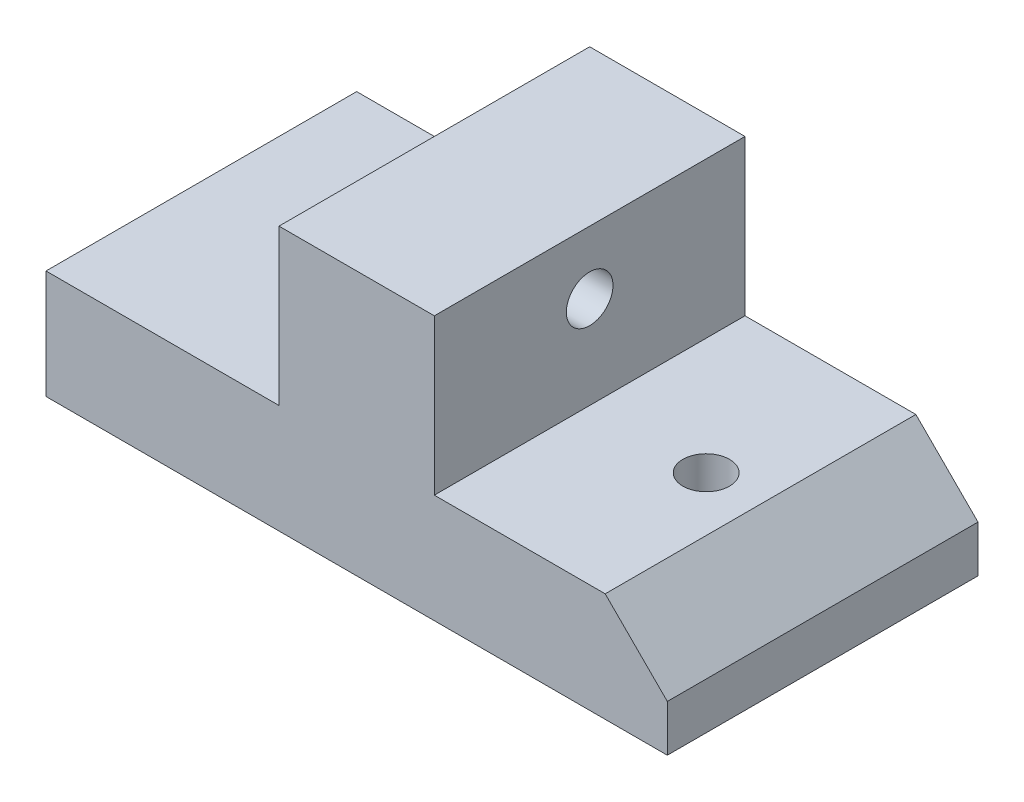
SolidWorks part; units mm, degrees
ref_plane "Front Plane" through (0, 0, 0) normal (0, 0, 1) x (1, 0, 0)
ref_plane "Top Plane" through (0, 0, 0) normal (0, 1, 0) x (1, 0, 0)
ref_plane "Right Plane" through (0, 0, 0) normal (1, 0, 0) x (0, 0, -1)
sketch "Sketch1" plane through (0, 0, 0) normal (0, 1, 0) x (1, 0, 0)
  line L5 (-34.4733, 11.0833) -> (5.5267, 11.0833)
  line L6 (-34.4733, 11.0833) -> (-34.4733, -8.9167)
  line L7 (-34.4733, -8.9167) -> (5.5267, -8.9167)
  line L8 (5.5267, 11.0833) -> (5.5267, -8.9167)
  dimension "D1" = 20
  dimension "D2" = 40
extrude "Boss-Extrude1" add sketch "Sketch1" along normal blind 4
sketch "Sketch2" plane through (0, 4, 0) normal (0, 1, 0) x (1, 0, 0)
  line L0 (-34.4733, -8.9167) -> (5.5267, 11.0833)
  line L1 (-34.4733, -8.9167) -> (5.5267, -8.9167) construction
  line L2 (-19.4733, 11.0833) -> (-9.4733, 11.0833)
  line L3 (-19.4733, 11.0833) -> (-19.4733, -8.9167)
  line L4 (-19.4733, -8.9167) -> (-9.4733, -8.9167)
  line L5 (-9.4733, 11.0833) -> (-9.4733, -8.9167)
  line L6 (-19.4733, 11.0833) -> (-9.4733, -8.9167) construction
  line L7 (-19.4733, -8.9167) -> (-9.4733, 11.0833) construction
  point P4 (-14.4733, 1.0833)
  dimension "D1" = 10
extrude "Boss-Extrude2" add sketch "Sketch2" along normal blind 10 contours L3 L2 L5 L4
sketch "Sketch3" plane through (-9.4733, 0, 0) normal (1, 0, 0) x (0, 0, -1)
  line L0 (-8.9167, 4) -> (11.0833, 4)
  line L1 (11.0833, 4) -> (1.0833, 4)
  circle A0 centre (1.0833, 9.951) radius 1.5
  dimension "D1" = 5.951
extrude "Cut-Extrude1" cut sketch "Sketch3" against normal blind 20 contours A0
sketch "Sketch4" plane through (0, 4, 0) normal (0, 1, 0) x (1, 0, 0)
  line L0 (-9.4733, -8.9167) -> (5.5267, 11.0833)
  line L1 (5.5267, 11.0833) -> (5.5267, -8.9167)
  circle A0 centre (-1.9733, 1.0833) radius 1.5
  circle A1 centre (-26.9733, 1.0833) radius 1.5
extrude "Cut-Extrude2" cut sketch "Sketch4" against normal blind 20 contours L0 A0 | L0 A0 | A1
sketch "Sketch5" plane through (0, 0, 8.9167) normal (0, 0, 1) x (1, 0, 0)
  line L0 (5.5267, 4) -> (1.5267, 4)
  line L1 (-9.4733, 4) -> (5.5267, 4) construction
  line L2 (1.5267, 4) -> (5.5267, 0)
extrude "Cut-Extrude3" cut sketch "Sketch5" against normal blind 20 and the other way through all
sketch "Sketch6" plane through (0, 0, 0) normal (0, -1, 0) x (1, 0, 0)
  line L1 (5.5267, 8.9167) -> (-34.4733, 8.9167)
  line L2 (5.5267, 8.9167) -> (5.5267, -11.0833)
  line L3 (5.5267, -11.0833) -> (-34.4733, -11.0833)
  line L4 (-34.4733, 8.9167) -> (-34.4733, -11.0833)
extrude "Boss-Extrude3" add sketch "Sketch6" along normal blind 4.5
sketch "Sketch7" plane through (0, 0, 0) normal (0, 1, 0) x (1, 0, 0)
  line L0 (-3.4733, 1.0833) -> (-0.4733, 1.0833)
  circle A0 centre (-1.9733, 1.0833) radius 1.5 construction
  circle A1 centre (-1.9733, 1.0833) radius 1.5 construction
  circle A2 centre (-1.9733, 1.0833) radius 1.5
extrude "Cut-Extrude5" cut sketch "Sketch7" against normal blind 4.5 contours A0 L0 | L0 A0
sketch "Sketch8" plane through (0, 4, 0) normal (0, 1, 0) x (1, 0, 0)
  line L0 (-28.4733, 1.0833) -> (-25.4733, 1.0833)
  circle A0 centre (-26.9733, 1.0833) radius 1.5 construction
  circle A1 centre (-26.9733, 1.0833) radius 1.5 construction
  circle A2 centre (-26.9733, 1.0833) radius 1.5
  circle M1 centre (-26.9733, 1.0833) radius 1.5
extrude "Cut-Extrude6" cut sketch "Sketch8" against normal blind 14.5 contours L0 M1 | L0 M1
sketch "Sketch9" plane through (0, -4.5, 0) normal (0, -1, 0) x (-1, 0, 0)
  line L1 (34.4733, -8.9167) -> (-5.5267, -8.9167)
  line L2 (34.4733, -8.9167) -> (34.4733, 11.0833)
  line L3 (34.4733, 11.0833) -> (-5.5267, 11.0833)
  line L4 (-5.5267, -8.9167) -> (-5.5267, 11.0833)
extrude "Cut-Extrude7" cut sketch "Sketch9" against normal blind 1.5
